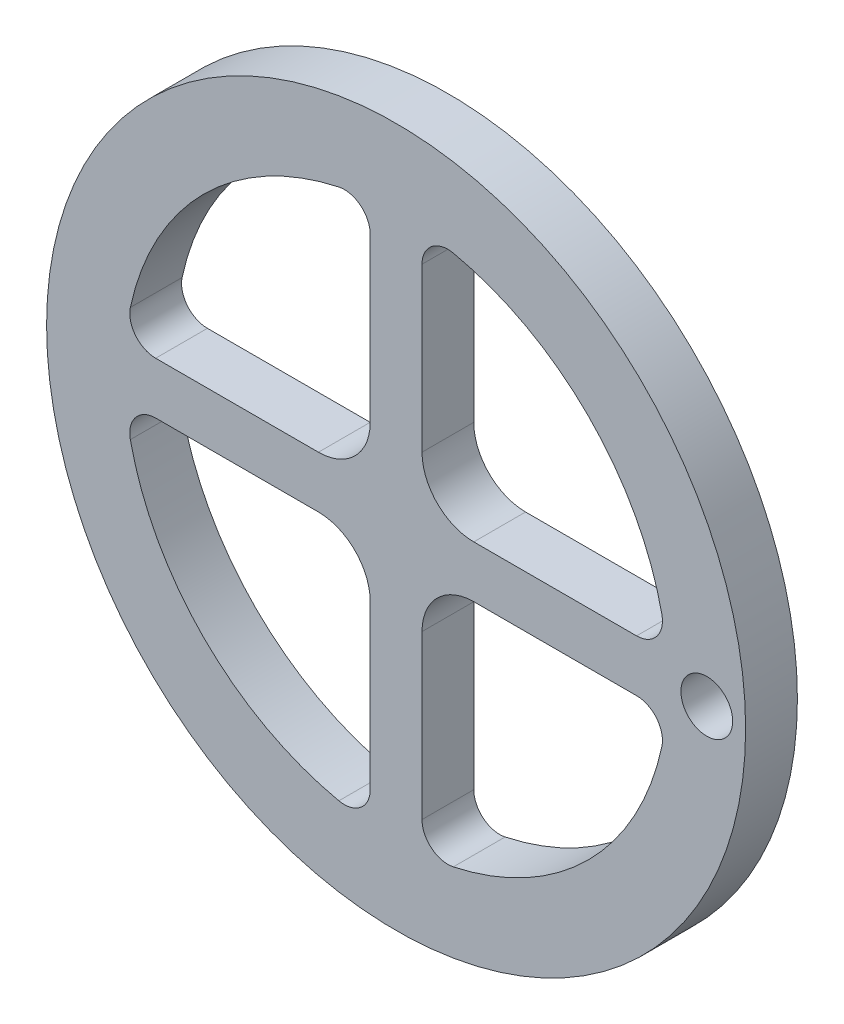
SolidWorks part; units mm, degrees
ref_plane "Front Plane" through (0, 0, 0) normal (0, 0, 1) x (1, 0, 0)
ref_plane "Top Plane" through (0, 0, 0) normal (0, 1, 0) x (1, 0, 0)
ref_plane "Right Plane" through (0, 0, 0) normal (1, 0, 0) x (0, 0, -1)
sketch "Sketch2" plane through (0, 0, 0) normal (0, 0, 1) x (1, 0, 0)
  line L3 (-2, 18.5742) -> (-2, 6)
  line L4 (18.5742, 2) -> (6, 2)
  line L5 (2, 18.5742) -> (2, 6)
  line L6 (18.5742, -2) -> (6, -2)
  line L12 (-6, 2) -> (-18.5742, 2)
  line L14 (2, -6) -> (2, -18.5742)
  line L15 (-6, -2) -> (-18.5742, -2)
  line L16 (-2, -6) -> (-2, -18.5742)
  arc A0 (-20.5294, -4.4211) -> (-4.4211, -20.5294) centre (0, 0) ccw
  circle A1 centre (0, 0) radius 27
  circle A2 centre (24, 0) radius 2
  arc A3 (-4.4211, 20.5294) -> (-20.5294, 4.4211) centre (0, 0) ccw
  arc A4 (4.4211, -20.5294) -> (20.5294, -4.4211) centre (0, 0) ccw
  arc A5 (20.5294, 4.4211) -> (4.4211, 20.5294) centre (0, 0) ccw
  arc A7 (-6, -2) -> (-2, -6) centre (-6, -6) cw
  arc A8 (2, -6) -> (6, -2) centre (6, -6) cw
  arc A9 (6, 2) -> (2, 6) centre (6, 6) cw
  arc A10 (-2, 6) -> (-6, 2) centre (-6, 6) cw
  arc A11 (-2, -18.5742) -> (-4.4211, -20.5294) centre (-4, -18.5742) cw
  arc A12 (4.4211, -20.5294) -> (2, -18.5742) centre (4, -18.5742) cw
  arc A13 (20.5294, -4.4211) -> (18.5742, -2) centre (18.5742, -4) ccw
  arc A14 (20.5294, 4.4211) -> (18.5742, 2) centre (18.5742, 4) cw
  arc A15 (4.4211, 20.5294) -> (2, 18.5742) centre (4, 18.5742) ccw
  arc A16 (-2, 18.5742) -> (-4.4211, 20.5294) centre (-4, 18.5742) ccw
  arc A17 (-18.5742, -2) -> (-20.5294, -4.4211) centre (-18.5742, -4) ccw
  arc A18 (-18.5742, 2) -> (-20.5294, 4.4211) centre (-18.5742, 4) cw
  point P8 (-2, -2)
  point P18 (-2, 2)
  point P32 (2, -20.9045)
  point P35 (20.9045, -2)
  point P38 (20.9045, 2)
  point P43 (-2, 20.9045)
  dimension "D1" = 4
  dimension "D2" = 2
extrude "Boss-Extrude1" add sketch "Sketch2" along normal blind 4
